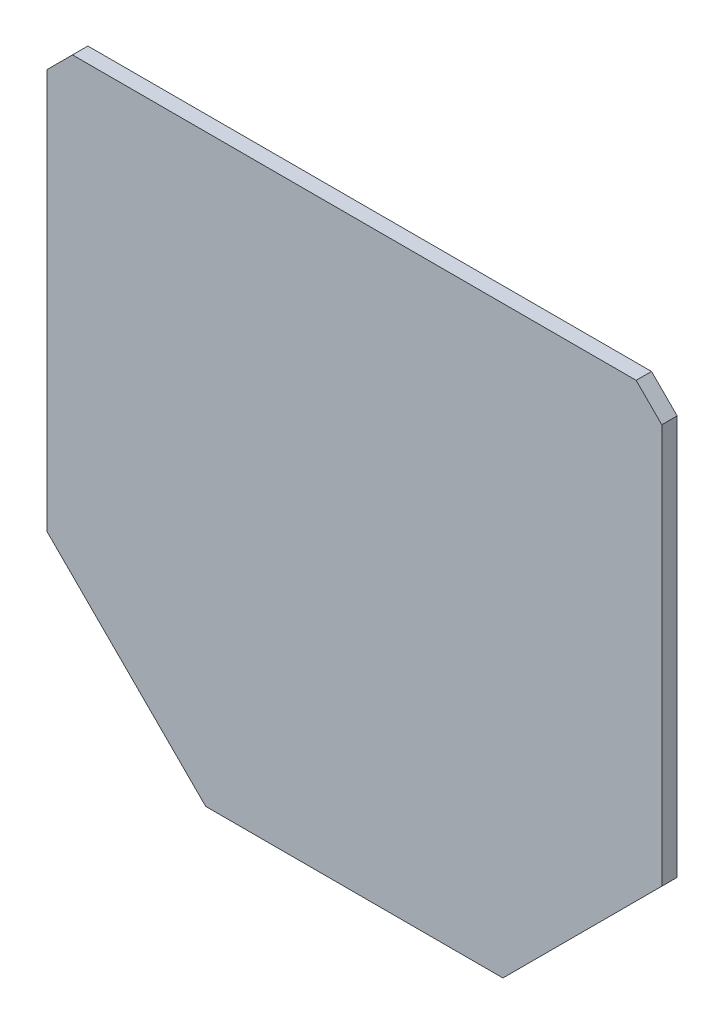
SolidWorks part; units mm, degrees
ref_plane "Front Plane" through (0, 0, 0) normal (0, 0, 1) x (1, 0, 0)
ref_plane "Top Plane" through (0, 0, 0) normal (0, 1, 0) x (1, 0, 0)
ref_plane "Right Plane" through (0, 0, 0) normal (1, 0, 0) x (0, 0, -1)
sketch "Sketch1" plane through (0, 0, 0) normal (0, 0, 1) x (1, 0, 0)
  line L0 (0, 0) -> (35, 14.4975) construction
  line L1 (35, 14.4975) -> (14.4975, 35) construction
  line L2 (14.4975, 35) -> (-14.4975, 35) construction
  line L3 (-14.4975, 35) -> (-35, 14.4975) construction
  line L4 (-35, 14.4975) -> (-35, -14.4975) construction
  line L5 (-35, -14.4975) -> (-14.4975, -35) construction
  line L6 (-14.4975, -35) -> (14.4975, -35) construction
  line L7 (14.4975, -35) -> (35, -14.4975) construction
  line L8 (35, -14.4975) -> (35, 14.4975) construction
  line L9 (0, 0) -> (0, 22) construction
  line L10 (0, 22) -> (27.4975, 22)
  line L11 (0, 0) -> (30, 0) construction
  line L12 (30, 0) -> (30, 19.4975)
  line L13 (30, 19.4975) -> (27.4975, 22)
  line L14 (30, 0) -> (30, -19.4975)
  line L15 (30, -19.4975) -> (14.4975, -35)
  line L16 (14.4975, -35) -> (-14.4975, -35)
  line L17 (0, -35) -> (-14.4975, -35)
  line L18 (-30, -19.4975) -> (-14.4975, -35)
  line L19 (-30, 0) -> (-30, 19.4975)
  line L20 (-30, 0) -> (-30, -19.4975)
  line L21 (0, 22) -> (-27.4975, 22)
  line L22 (-27.4975, 22) -> (-30, 19.4975)
  circle A0 centre (0, 0) radius 35 construction
  dimension "D1" = 22
  dimension "D2" = 30
extrude "Boss-Extrude1" add sketch "Sketch1" along normal blind 1.5 contours L21 L22 L19 L20 L18 L16 L15 L14 L12 L13 L10
